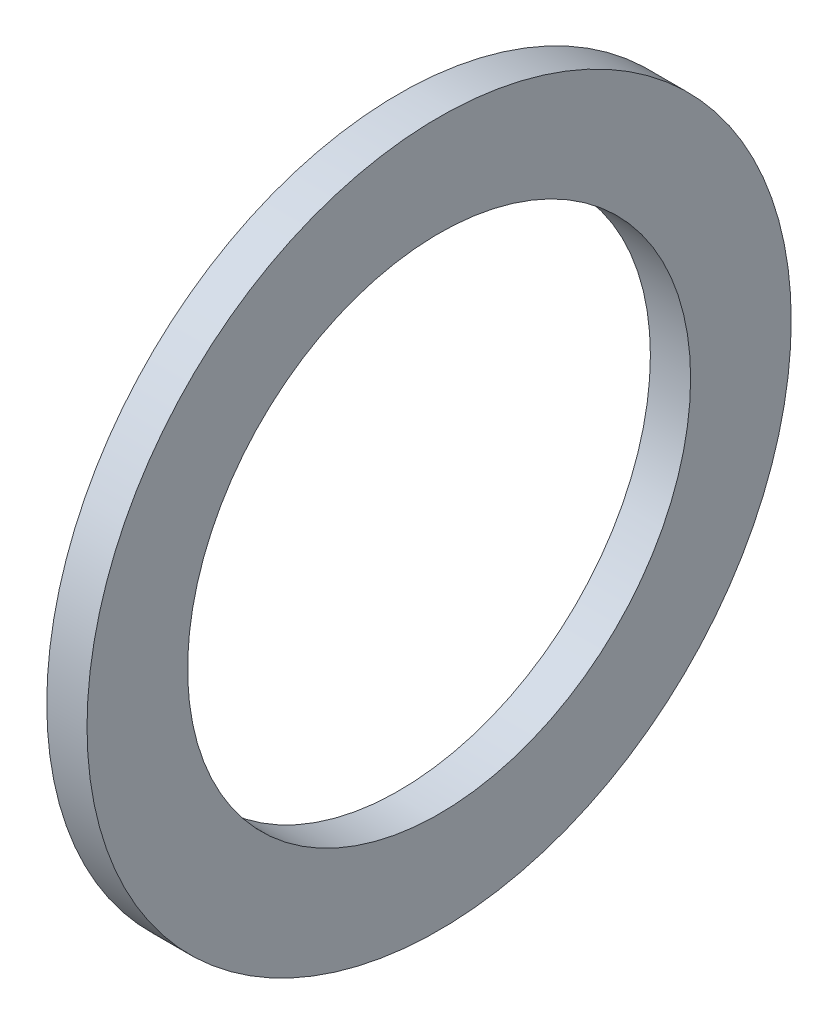
SolidWorks part; units mm, degrees
material "1.7218 (25CrMo4)"
ref_plane "Płaszczyzna XY" through (0, 0, 0) normal (0, 0, 1) x (1, 0, 0)
ref_plane "Płaszczyzna XZ" through (0, 0, 0) normal (0, 1, 0) x (1, 0, 0)
ref_plane "Płaszczyzna YZ" through (0, 0, 0) normal (1, 0, 0) x (0, 0, -1)
sketch "Szkic1" plane through (0, 0, 0) normal (1, 0, 0) x (0, 0, -1)
  circle A0 centre (0, 0) radius 17.5
  circle A1 centre (0, 0) radius 12.5
  dimension "D1" = 25
  dimension "D2" = 35
extrude "Dodanie-wyciągnięcie1" add sketch "Szkic1" along normal blind 2
